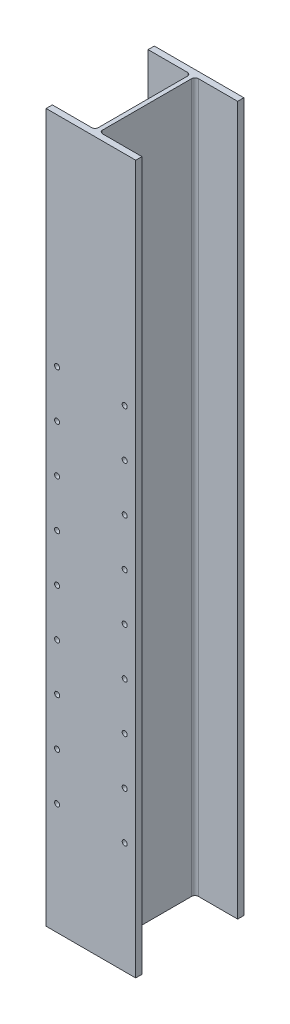
SolidWorks part; units mm, degrees
ref_plane "Front Plane" through (0, 0, 0) normal (0, 0, 1) x (1, 0, 0)
ref_plane "Top Plane" through (0, 0, 0) normal (0, 1, 0) x (1, 0, 0)
ref_plane "Right Plane" through (0, 0, 0) normal (1, 0, 0) x (0, 0, -1)
sketch "Sketch1" plane through (0, 0, 0) normal (0, 1, 0) x (1, 0, 0)
  line L0 (-84.1375, 101.6) -> (84.1375, 101.6)
  line L1 (84.1375, -89.916) -> (84.1375, -101.6)
  line L2 (84.1375, -89.916) -> (10.3188, -89.916)
  line L3 (3.9688, -83.566) -> (3.9688, 83.566)
  line L4 (-10.3188, 89.916) -> (-84.1375, 89.916)
  line L5 (-3.9687, 83.566) -> (-3.9687, -83.566)
  line L6 (-10.3188, -89.916) -> (-84.1375, -89.916)
  line L7 (-84.1375, -89.916) -> (-84.1375, -101.6)
  line L8 (-84.1375, 89.916) -> (-84.1375, 101.6)
  line L9 (-84.1375, -101.6) -> (84.1375, -101.6)
  line L10 (84.1375, 101.6) -> (84.1375, 89.916)
  line L11 (84.1375, 89.916) -> (10.3188, 89.916)
  line L12 (0, 101.6) -> (0, 0) construction
  line L13 (3.9688, 0) -> (0, 0) construction
  arc A0 (-10.3188, -89.916) -> (-3.9687, -83.566) centre (-10.3187, -83.566) ccw
  arc A1 (10.3188, -89.916) -> (3.9688, -83.566) centre (10.3188, -83.566) cw
  arc A2 (3.9688, 83.566) -> (10.3188, 89.916) centre (10.3187, 83.566) cw
  arc A3 (-3.9687, 83.566) -> (-10.3188, 89.916) centre (-10.3187, 83.566) ccw
  dimension "D5" = 6.35
  dimension "D1" = 168.275
  dimension "D2" = 203.2
  dimension "D3" = 11.684
  dimension "D4" = 7.9375
extrude "Boss-Extrude1" add sketch "Sketch1" along normal mid plane 1330.325
sketch "Sketch2" plane through (0, 0, 101.6) normal (0, 0, 1) x (1, 0, 0)
  line L0 (0, 665.1625) -> (0, -665.1625) construction
  line L1 (-84.1375, 665.1625) -> (84.1375, 665.1625) construction
  line L2 (-84.1375, -665.1625) -> (84.1375, -665.1625) construction
hole_wizard "3/8 (0.375) Diameter Hole1" positions "Sketch4" profile "Sketch3" hole size "3/8" standard "ANSI Inch" end condition up to next
sketch "Sketch4" plane through (0, 0, 101.6) normal (0, 0, 1) x (1, 0, 0)
  line L0 (-63.5, 255.5875) -> (-63.5, -665.1625) construction
  line L1 (-84.1375, -665.1625) -> (84.1375, -665.1625) construction
  line L2 (63.5, 255.5875) -> (63.5, -665.1625) construction
  line L3 (0, -665.1625) -> (0, 255.5875) construction
  line L4 (-63.5, 255.5875) -> (63.5, 255.5875) construction
  line L5 (-63.5, -455.6125) -> (63.5, -455.6125) construction
  line L6 (-63.5, -366.7125) -> (63.5, -366.7125) construction
  line L7 (-63.5, -277.8125) -> (63.5, -277.8125) construction
  line L8 (-63.5, -188.9125) -> (63.5, -188.9125) construction
  line L9 (-63.5, -100.0125) -> (63.5, -100.0125) construction
  line L10 (-63.5, -11.1125) -> (63.5, -11.1125) construction
  line L11 (-63.5, 77.7875) -> (63.5, 77.7875) construction
  line L12 (-63.5, 166.6875) -> (63.5, 166.6875) construction
  point P1 (-63.5, 255.5875)
  point P5 (63.5, 255.5875)
  point P14 (63.5, -455.6125)
  point P16 (63.5, -366.7125)
  point P18 (63.5, -277.8125)
  point P20 (63.5, -188.9125)
  point P22 (63.5, -100.0125)
  point P24 (63.5, -11.1125)
  point P26 (63.5, 77.7875)
  point P31 (-63.5, -455.6125)
  point P33 (-63.5, -366.7125)
  point P35 (-63.5, -277.8125)
  point P37 (-63.5, -188.9125)
  point P39 (-63.5, -100.0125)
  point P41 (-63.5, -11.1125)
  point P43 (-63.5, 77.7875)
  point P77 (-63.5, 166.6875)
  point P79 (63.5, 166.6875)
  dimension "D1" = 127
  dimension "D2" = 88.9
  dimension "D3" = 88.9
  dimension "D4" = 88.9
  dimension "D5" = 88.9
  dimension "D6" = 88.9
  dimension "D7" = 88.9
  dimension "D8" = 88.9
  dimension "D9" = 209.55
  dimension "D10" = 88.9
sketch "Sketch3" plane through (-63.5, 255.5875, 101.6) normal (1, 0, 0) x (0, -1, 0)
  line L0 (0, 0) -> (0, 11.684)
  line L1 (0, 11.684) -> (4.7625, 11.684)
  line L2 (4.7625, 11.684) -> (4.7625, 0)
  line L5 (4.7625, 0) -> (0, 0)
  line L11 (0, -6.35) -> (0, 107.95) construction
  dimension "Thru Hole Dia." = 9.525
  dimension "Thru Hole Depth" = 11.684
